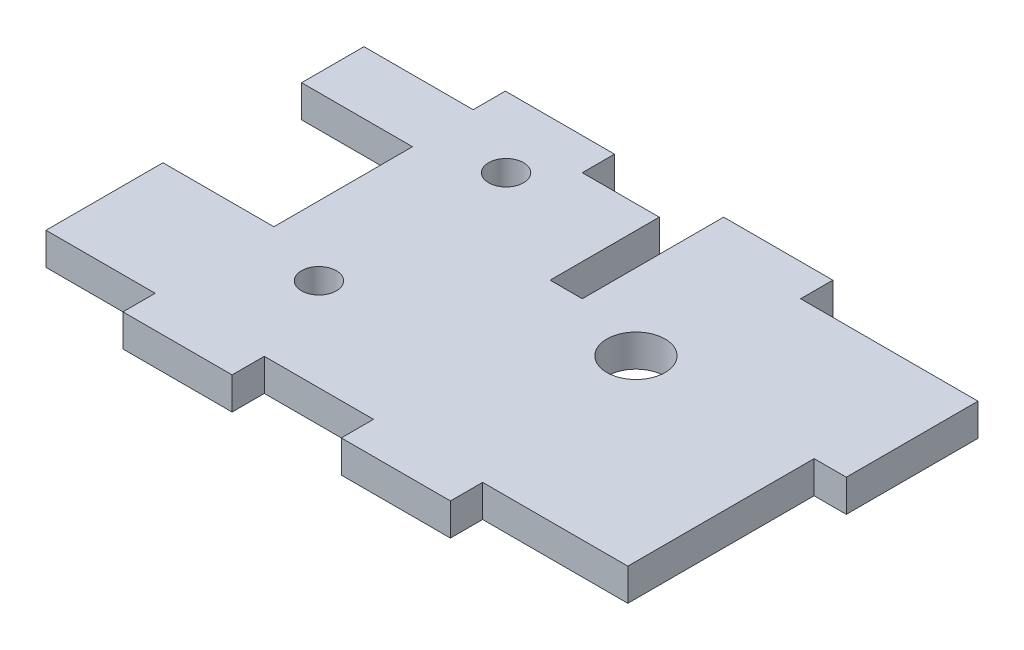
SolidWorks part; units mm, degrees
ref_plane "Front Plane" through (0, 0, 0) normal (0, 0, 1) x (1, 0, 0)
ref_plane "Top Plane" through (0, 0, 0) normal (0, 1, 0) x (1, 0, 0)
ref_plane "Right Plane" through (0, 0, 0) normal (1, 0, 0) x (0, 0, -1)
sketch "Sketch1" plane through (0, 0, 0) normal (0, 1, 0) x (1, 0, 0)
  line L1 (-24.1554, 15.015) -> (24.1554, 15.015)
  line L2 (-24.1554, 15.015) -> (-24.1554, -15.015)
  line L3 (-24.1554, -15.015) -> (24.1554, -15.015)
  line L4 (24.1554, 15.015) -> (24.1554, -15.015)
  line L5 (-24.1554, 15.015) -> (24.1554, -15.015) construction
  line L6 (-24.1554, -15.015) -> (24.1554, 15.015) construction
  point P0 (0, 0)
  dimension "D1" = 48.3108
  dimension "D2" = 30.03
extrude "Boss-Extrude1" add sketch "Sketch1" along normal blind 2.95
sketch "Sketch2" plane through (0, 2.95, 0) normal (0, 1, 0) x (1, 0, 0)
  line L0 (-24.1554, 15.015) -> (-24.1554, -15.015) construction
  line L1 (-24.1554, 6.35) -> (-13.9954, 6.35)
  line L2 (-24.1554, 6.35) -> (-24.1554, -6.35)
  line L3 (-24.1554, -6.35) -> (-13.9954, -6.35)
  line L4 (-13.9954, 6.35) -> (-13.9954, -6.35)
  line L5 (-24.1554, 6.35) -> (-13.9954, -6.35) construction
  line L6 (-24.1554, -6.35) -> (-13.9954, 6.35) construction
  point P0 (-19.0754, 0)
  dimension "D1" = 12.7
  dimension "D2" = 10.16
extrude "Cut-Extrude1" cut sketch "Sketch2" against normal through all
hole_wizard "M3 Clearance Hole1" positions "Sketch3" profile "Sketch5" hole size "M3" standard "ANSI Metric" end condition through all
sketch "Sketch3" plane through (0, 2.95, 0) normal (0, 1, 0) x (1, 0, 0)
  line L0 (-7.6454, -8.5725) -> (-7.6454, 8.5725)
  line L2 (-24.1554, 15.015) -> (-24.1554, 6.35) construction
  point P0 (-7.6454, 8.5725)
  point P2 (-7.6454, -8.5725)
  point P11 (-7.6454, 0)
  dimension "D1" = 17.145
  dimension "D2" = 16.51
sketch "Sketch5" plane through (-7.6454, 2.95, -8.5725) normal (1, 0, 0) x (0, 0, 1)
  line L0 (0, 0) -> (0, 2.95)
  line L1 (0, 2.95) -> (1.6, 2.95)
  line L2 (1.6, 2.95) -> (1.6, 0)
  line L5 (1.6, 0) -> (0, 0)
  line L11 (0, -6.35) -> (0, 107.95) construction
  dimension "Thru Hole Dia." = 3.2
  dimension "Thru Hole Depth" = 2.95
sketch "Sketch7" plane through (0, 0, 15.015) normal (0, 0, 1) x (1, 0, 0)
  line L4 (-24.1554, 0) -> (24.1554, 0)
  line L5 (24.1554, 0) -> (24.1554, 2.95)
  line L6 (24.1554, 2.95) -> (-24.1554, 2.95)
  line L7 (-24.1554, 2.95) -> (-24.1554, 0)
  line L8 (-24.1554, 0) -> (24.1554, 0)
  line L9 (24.1554, 0) -> (24.1554, 2.95)
  line L10 (24.1554, 2.95) -> (-24.1554, 2.95)
  line L11 (-24.1554, 2.95) -> (-24.1554, 0)
  dimension "D1" = 0
extrude "Boss-Extrude2" add sketch "Sketch7" along normal blind 5
ref_plane "Plane1" through (0, 0, 2.5) normal (0, 0, 1) x (1, 0, 0)
sketch "Sketch6" plane through (0, 2.95, 0) normal (0, 1, 0) x (1, 0, 0)
  line L1 (-24.1554, -20.015) -> (-14.1554, -20.015)
  line L2 (-24.1554, -20.015) -> (-24.1554, -17.065)
  line L3 (-24.1554, -17.065) -> (-14.1554, -17.065)
  line L4 (-14.1554, -20.015) -> (-14.1554, -17.065)
  line L5 (-24.1554, -20.015) -> (-14.1554, -17.065) construction
  line L6 (-24.1554, -17.065) -> (-14.1554, -20.015) construction
  point P4 (-19.1554, -18.54)
  dimension "D1" = 10
  dimension "D2" = 2.95
extrude "Cut-Extrude2" cut sketch "Sketch6" against normal through all
pattern_linear "LPattern1" count 3 spacing 20 along (1, 0, 0) of "Cut-Extrude2"
mirror "Mirror1" about plane through (0, 0, 2.5) normal (0, 0, 1) of "LPattern1", "Cut-Extrude2"
sketch "Sketch8" plane through (24.1554, 0, 0) normal (1, 0, 0) x (0, 0, -1)
  line L1 (12.065, 2.95) -> (0, 2.95)
  line L2 (12.065, 2.95) -> (12.065, 0)
  line L3 (12.065, 0) -> (0, 0)
  line L4 (0, 2.95) -> (0, 0)
  line L5 (12.065, 2.95) -> (0, 0) construction
  line L6 (12.065, 0) -> (0, 2.95) construction
  point P4 (6.0325, 1.475)
extrude "Boss-Extrude3" add sketch "Sketch8" along normal up to surface (7.9392 mm away)
sketch "Sketch9" plane through (24.1554, 0, 0) normal (1, 0, 0) x (0, 0, -1)
  line L4 (0, 0) -> (0, 2.95)
  line L5 (0, 2.95) -> (-17.065, 2.95)
  line L6 (-17.065, 2.95) -> (-17.065, 0)
  line L7 (-17.065, 0) -> (0, 0)
  line L8 (0, 0) -> (0, 2.95)
  line L9 (0, 2.95) -> (-17.065, 2.95)
  line L10 (-17.065, 2.95) -> (-17.065, 0)
  line L11 (-17.065, 0) -> (0, 0)
  dimension "D1" = 0
extrude "Boss-Extrude4" add sketch "Sketch9" along normal up to surface (4.9892 mm away)
sketch "Sketch10" plane through (0, 0, 0) normal (0, -1, 0) x (1, 0, 0)
  line L0 (-7.6454, 8.5725) -> (-7.6454, -8.5725) construction
  line L1 (-7.6454, 0) -> (12.827, 0) construction
  circle A0 centre (-7.6454, -8.5725) radius 1.6 construction
  circle A1 centre (-7.6454, 8.5725) radius 1.6 construction
  circle A2 centre (-7.6454, -8.5725) radius 1.6 construction
  circle A3 centre (-7.6454, 8.5725) radius 1.6 construction
  circle A4 centre (12.827, 0) radius 2.667
  dimension "D2" = 5.334
  dimension "D1" = 20.4724
extrude "Cut-Extrude3" cut sketch "Sketch10" against normal through all
sketch "Sketch11" plane through (0, 0, 0) normal (0, -1, 0) x (1, 0, 0)
  line L0 (5.8446, -15.015) -> (5.8446, -12.065) construction
  line L1 (5.8446, -15.015) -> (5.8446, 17.065) construction
  line L3 (5.8446, -12.065) -> (2.8946, -12.065)
  line L4 (5.8446, -12.065) -> (5.8446, -2.065)
  line L5 (5.8446, -2.065) -> (2.8946, -2.065)
  line L6 (2.8946, -12.065) -> (2.8946, -2.065)
  line L7 (5.8446, -12.065) -> (2.8946, -2.065) construction
  line L8 (5.8446, -2.065) -> (2.8946, -12.065) construction
  line L28 (-14.1554, -12.065) -> (-14.1554, -15.015)
  line L29 (-14.1554, -15.015) -> (-4.1554, -15.015)
  line L30 (-4.1554, -15.015) -> (-4.1554, -12.065)
  line L31 (-4.1554, -12.065) -> (5.8446, -12.065)
  line L32 (5.8446, -12.065) -> (5.8446, -15.015)
  line L33 (5.8446, -15.015) -> (15.8446, -15.015)
  line L34 (15.8446, -15.015) -> (15.8446, -12.065)
  line L35 (15.8446, -12.065) -> (32.0946, -12.065)
  line L36 (32.0946, -12.065) -> (32.0946, 0)
  line L37 (32.0946, 0) -> (29.1446, 0)
  line L38 (29.1446, 0) -> (29.1446, 17.065)
  line L39 (29.1446, 17.065) -> (15.8446, 17.065)
  line L40 (15.8446, 17.065) -> (15.8446, 20.015)
  line L41 (15.8446, 20.015) -> (5.8446, 20.015)
  line L42 (5.8446, 20.015) -> (5.8446, 17.065)
  line L43 (5.8446, 17.065) -> (-4.1554, 17.065)
  line L44 (-4.1554, 17.065) -> (-4.1554, 20.015)
  line L45 (-4.1554, 20.015) -> (-14.1554, 20.015)
  line L46 (-14.1554, 20.015) -> (-14.1554, 17.065)
  line L47 (-14.1554, 17.065) -> (-24.1554, 17.065)
  line L48 (-24.1554, 17.065) -> (-24.1554, 6.35)
  line L49 (-24.1554, 6.35) -> (-13.9954, 6.35)
  line L50 (-13.9954, 6.35) -> (-13.9954, -6.35)
  line L51 (-13.9954, -6.35) -> (-24.1554, -6.35)
  line L52 (-24.1554, -6.35) -> (-24.1554, -12.065)
  line L53 (-24.1554, -12.065) -> (-14.1554, -12.065)
  line L54 (-14.1554, -12.065) -> (-14.1554, -15.015) construction
  line L55 (-14.1554, -15.015) -> (-4.1554, -15.015) construction
  line L56 (-4.1554, -15.015) -> (-4.1554, -12.065) construction
  line L57 (-4.1554, -12.065) -> (5.8446, -12.065) construction
  line L58 (5.8446, -12.065) -> (5.8446, -15.015) construction
  line L59 (5.8446, -15.015) -> (15.8446, -15.015) construction
  line L60 (15.8446, -15.015) -> (15.8446, -12.065) construction
  line L61 (15.8446, -12.065) -> (32.0946, -12.065) construction
  line L62 (32.0946, -12.065) -> (32.0946, 0) construction
  line L63 (32.0946, 0) -> (29.1446, 0) construction
  line L64 (29.1446, 0) -> (29.1446, 17.065) construction
  line L65 (29.1446, 17.065) -> (15.8446, 17.065) construction
  line L66 (15.8446, 17.065) -> (15.8446, 20.015) construction
  line L67 (15.8446, 20.015) -> (5.8446, 20.015) construction
  line L68 (5.8446, 20.015) -> (5.8446, 17.065) construction
  line L69 (5.8446, 17.065) -> (-4.1554, 17.065) construction
  line L70 (-4.1554, 17.065) -> (-4.1554, 20.015) construction
  line L71 (-4.1554, 20.015) -> (-14.1554, 20.015) construction
  line L72 (-14.1554, 20.015) -> (-14.1554, 17.065) construction
  line L73 (-14.1554, 17.065) -> (-24.1554, 17.065) construction
  line L74 (-24.1554, 17.065) -> (-24.1554, 6.35) construction
  line L75 (-24.1554, 6.35) -> (-13.9954, 6.35) construction
  line L76 (-13.9954, 6.35) -> (-13.9954, -6.35) construction
  line L77 (-13.9954, -6.35) -> (-24.1554, -6.35) construction
  line L78 (-24.1554, -6.35) -> (-24.1554, -12.065) construction
  line L79 (-24.1554, -12.065) -> (-14.1554, -12.065) construction
  point P29 (4.3696, -7.065)
  dimension "D2" = 2.95
  dimension "D3" = 10
extrude "Cut-Extrude4" cut sketch "Sketch11" against normal through all
equation "\"wood\"= 2.95mm"
equation "\"slot_width\"= 10mm"
equation "\"slot_offset\"= 10mm"
equation "\"D2@Sketch1\"=.95in +2 * \"wood\""
equation "\"D1@Boss-Extrude1\"=\"wood\""
equation "\"D1@Sketch6\"=\"slot_width\""
equation "\"D2@Sketch6\"=\"wood\""
equation "\"D3@LPattern1\"=2 * \"slot_offset\""
equation "\"D2@Sketch11\"=\"wood\""
equation "\"D3@Sketch11\"=\"slot_width\""
